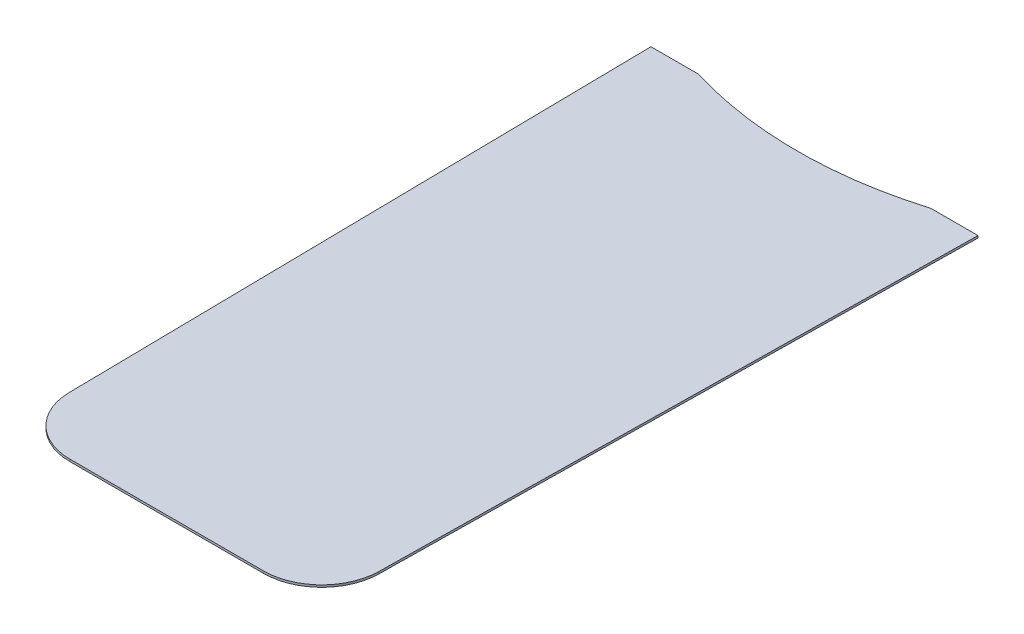
SolidWorks part; units mm, degrees
material "PVC hart"
ref_plane "Ebene vorne" through (0, 0, 0) normal (0, 0, 1) x (1, 0, 0)
ref_plane "Ebene oben" through (0, 0, 0) normal (0, 1, 0) x (1, 0, 0)
ref_plane "Ebene rechts" through (0, 0, 0) normal (1, 0, 0) x (0, 0, -1)
sketch "Skizze1" plane through (0, 0, 0) normal (0, 1, 0) x (1, 0, 0)
  line L0 (0, 73.25) -> (0, -73.25) construction
  line L1 (-36, 77.25) -> (-27, 77.25)
  line L2 (-36, 77.25) -> (-36, -59.75)
  line L3 (36, 77.25) -> (27, 77.25)
  line L4 (36, 77.25) -> (36, -59.75)
  line L5 (-22.5, -73.25) -> (22.5, -73.25)
  arc A0 (-36, -59.75) -> (-22.5, -73.25) centre (-22.5, -59.75) ccw
  arc A1 (22.5, -73.25) -> (36, -59.75) centre (22.5, -59.75) ccw
  arc A2 (-27, 77.25) -> (27, 77.25) centre (0, 166.375) ccw
  dimension "D1" = 72
  dimension "D2" = 45
  dimension "D3" = 137
  dimension "D4" = 4
  dimension "D5" = 54
extrude "Aufsatz-Linear austragen1" add sketch "Skizze1" against normal mid plane 0.5
sketch "Skizze2" plane through (0, 0.25, 0) normal (0, 1, 0) x (1, 0, 0)
  line L0 (-35.9986, -59.9469) -> (-38, 77.25)
  line L1 (-38, 77.25) -> (-36, 77.25)
  line L2 (0, 73.25) -> (0, -73.25) construction
  line L3 (-22.5, -73.25) -> (22.5, -73.25) construction
  line L4 (-36, 77.25) -> (-36, -59.75) construction
  line L5 (-36, 77.25) -> (-36, -59.75)
  line L6 (36, 77.25) -> (36, -59.75)
  line L7 (38, 77.25) -> (36, 77.25)
  line L8 (35.9986, -59.9469) -> (38, 77.25)
  arc A0 (-36, -59.75) -> (-22.5, -73.25) centre (-22.5, -59.75) ccw construction
  arc A1 (-27, 77.25) -> (27, 77.25) centre (0, 166.375) ccw construction
  arc A2 (-36, -59.75) -> (-35.9986, -59.9469) centre (-22.5, -59.75) ccw
  arc A3 (36, -59.75) -> (35.9986, -59.9469) centre (22.5, -59.75) cw
  dimension "D1" = 2
extrude "Aufsatz-Linear austragen2" add sketch "Skizze2" against normal up to surface (0.5 mm away)
